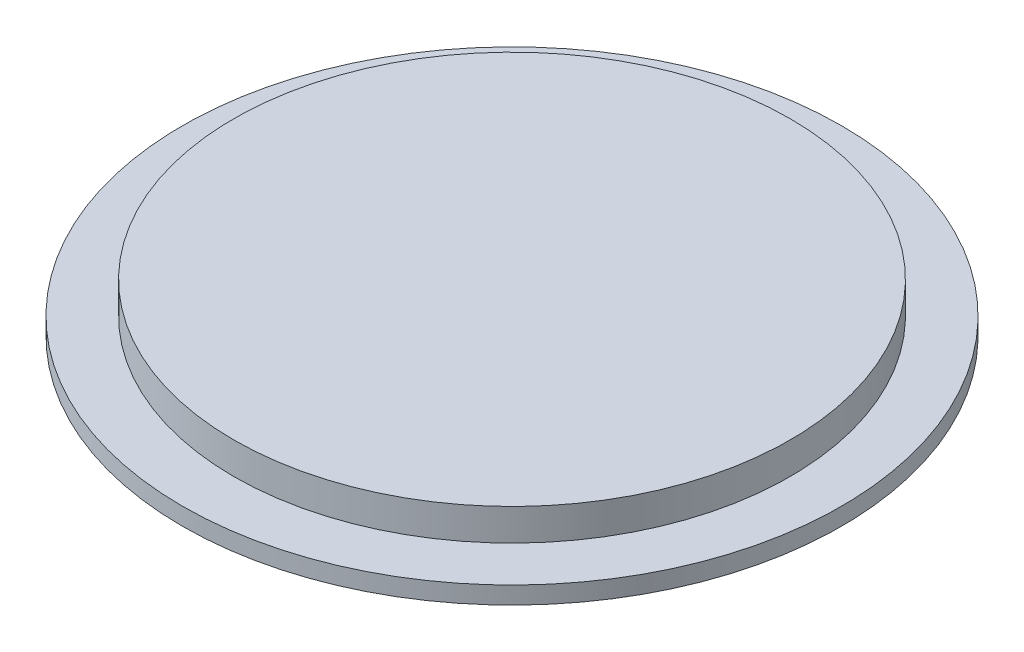
SolidWorks part; units mm, degrees
ref_plane "Front Plane" through (0, 0, 0) normal (0, 0, 1) x (1, 0, 0)
ref_plane "Top Plane" through (0, 0, 0) normal (0, 1, 0) x (1, 0, 0)
ref_plane "Right Plane" through (0, 0, 0) normal (1, 0, 0) x (0, 0, -1)
sketch "Sketch1" plane through (0, 0, 0) normal (0, 1, 0) x (1, 0, 0)
  circle A0 centre (0, 0) radius 16.256
  dimension "D1" = 32.512
extrude "Boss-Extrude1" add sketch "Sketch1" along normal blind 2.8702
sketch "Sketch2" plane through (0, 0, 0) normal (0, -1, 0) x (1, 0, 0)
  circle A2 centre (0, 0) radius 19.256
  circle A3 centre (0, 0) radius 19.256
  dimension "D1" = 3
extrude "Boss-Extrude2" add sketch "Sketch2" against normal blind 1.016 contours A3
